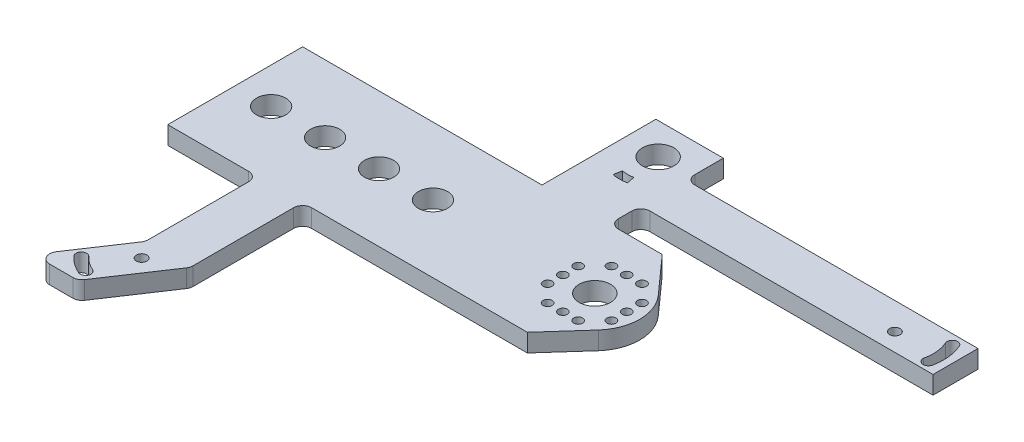
SolidWorks part; units mm, degrees
ref_plane "Front Plane" through (0, 0, 0) normal (0, 0, 1) x (1, 0, 0)
ref_plane "Top Plane" through (0, 0, 0) normal (0, 1, 0) x (1, 0, 0)
ref_plane "Right Plane" through (0, 0, 0) normal (1, 0, 0) x (0, 0, -1)
sketch "Sketch1" plane through (0, 0, 0) normal (0, 1, 0) x (1, 0, 0)
  circle A0 centre (0, 0) radius 10
  dimension "D1" = 20
extrude "Boss-Extrude1" add sketch "Sketch1" along normal blind 4
sketch "Sketch2" plane through (0, 0, 0) normal (0, 1, 0) x (1, 0, 0)
  line L0 (0, 0) -> (-40, 0) construction
  line L1 (-80, 15) -> (0, 15)
  line L2 (-80, 15) -> (-80, -15)
  line L3 (0, 15) -> (0, -15)
  line L4 (-80, -15) -> (0, -15)
  line L5 (0, 0) -> (-80, 0) construction
  line L6 (-40, 15) -> (-40, -15) construction
  line L7 (0, 15) -> (7.4536, 6.6667)
  line L8 (0, -15) -> (7.4536, -6.6667)
  line L9 (7.4536, 6.6667) -> (7.4536, -6.6667)
  circle A0 centre (0, 0) radius 10 construction
  dimension "D1" = 30
  dimension "D2" = 80
extrude "Boss-Extrude2" add sketch "Sketch2" along normal blind 4 contours L2 L4 L3 L1 | L9 L7 L3 L8
sketch "Sketch5" plane through (0, 0, 0) normal (0, 1, 0) x (1, 0, 0)
  line L0 (0, 0) -> (-19.25, 33.342) construction
  line L1 (-19.25, 33.342) -> (-19.25, 15) construction
  line L2 (-80, 15) -> (0, 15) construction
  line L3 (0, 0) -> (-80, 0) construction
  line L4 (-11.75, 40.342) -> (-26.75, 40.342)
  line L5 (-11.75, 40.342) -> (-11.75, 15)
  line L6 (-11.75, 15) -> (-26.75, 15)
  line L7 (-26.75, 40.342) -> (-26.75, 15)
  line L8 (-19.25, 15) -> (-19.25, 40.342) construction
  line L9 (-11.75, 27.671) -> (-26.75, 27.671) construction
  line L10 (-80, 15) -> (-80, -15) construction
  circle A0 centre (-19.25, 33.342) radius 11 construction
  circle A1 centre (0, 0) radius 27.5 construction
  circle A2 centre (-19.25, 33.342) radius 3.5
  point P5 (-19.25, 27.671)
  dimension "D2" = 22
  dimension "D3" = 55
  dimension "D7" = 7
  dimension "D1" = 38.5
  dimension "D4" = 15
  dimension "D5" = 7
  dimension "D6" = 60
extrude "Boss-Extrude3" add sketch "Sketch5" along normal blind 4
sketch "Sketch6" plane through (0, 4, 0) normal (0, 1, 0) x (1, 0, 0)
  line L0 (-19.25, 33.342) -> (-19.25, 25.012) construction
  line L1 (-20.6, 25.1221) -> (-20.3893, 26.4049) construction
  line L2 (-19.25, 25.012) -> (-19.25, 26.312) construction
  line L3 (-20.85, 24.9125) -> (-20.5143, 26.6809)
  line L4 (-19.25, 24.762) -> (-19.25, 26.562)
  circle A0 centre (-19.25, 33.342) radius 8.33 construction
  arc A1 (-19.25, 25.012) -> (-20.6, 25.1221) centre (-19.25, 33.342) cw construction
  arc A2 (-19.25, 26.312) -> (-20.3893, 26.4049) centre (-19.25, 33.342) cw construction
  arc A3 (-19.25, 24.762) -> (-20.85, 24.9125) centre (-19.25, 33.342) cw
  arc A4 (-19.25, 26.562) -> (-20.5143, 26.6809) centre (-19.25, 33.342) cw
  point P11 (0, 0)
  point P13 (0, 0)
  point P14 (0, 0)
  point P15 (-21.0225, 26.9125)
  dimension "D1" = 16.66
  dimension "D2" = 1.3
  dimension "D3" = 1.35
  dimension "D4" = 0.25
  dimension "D5" = 0.25
  dimension "D6" = 0.25
extrude "Cut-Extrude1" cut sketch "Sketch6" against normal through all contours L3 A4 L4 A3
ref_plane "Plane1" through (-19.25, 0, 0) normal (-1, 0, 0) x (0, 0, 1)
mirror "Mirror1" about plane through (-19.25, 0, 0) normal (-1, 0, 0) of "Cut-Extrude1"
sketch "Sketch7" plane through (0, 4, 0) normal (0, 1, 0) x (1, 0, 0)
  line L0 (-80, 0) -> (10, 0) construction
  line L1 (-80, 15) -> (-80, -15) construction
  arc A0 (7.4536, -6.6667) -> (7.4536, 6.6667) centre (0, 0) ccw construction
  circle A1 centre (-72, 0) radius 3.25
  dimension "D1" = 6.5
  dimension "D2" = 8
extrude "Cut-Extrude2" cut sketch "Sketch7" against normal through all
pattern_linear "LPattern1" count 4 spacing 12 along (1, 0, 0) of "Cut-Extrude2"
sketch "Sketch8" plane through (0, 0, 0) normal (0, 1, 0) x (1, 0, 0)
  line L0 (-26.75, 27) -> (20.75, 27) construction
  line L1 (-26.75, 40.342) -> (-26.75, 15) construction
  line L2 (-11.75, 15) -> (-11.75, 40.342) construction
  line L3 (53.25, 22) -> (-11.75, 22)
  line L4 (53.25, 22) -> (53.25, 32)
  line L5 (53.25, 32) -> (-11.75, 32)
  line L6 (-11.75, 22) -> (-11.75, 32)
  line L7 (20.75, 32) -> (20.75, 22) construction
  line L8 (53.25, 27) -> (-11.75, 27) construction
  line L9 (-80, 15) -> (-26.75, 15) construction
  dimension "D1" = 65
  dimension "D2" = 10
  dimension "D3" = 12
extrude "Boss-Extrude4" add sketch "Sketch8" along normal blind 4
sketch "Sketch9" plane through (0, 4, 0) normal (0, 1, 0) x (1, 0, 0)
  line L0 (53.25, 26) -> (40.75, 26) construction
  line L1 (53.25, 22) -> (53.25, 32) construction
  line L2 (-11.75, 22) -> (53.25, 22) construction
  line L3 (48.5662, 29.4302) -> (50.7181, 30.3746) construction
  line L4 (51.4453, 23.9728) -> (49.0547, 24.0272) construction
  circle A0 centre (40.75, 26) radius 1.175
  arc A1 (50.7181, 30.3746) -> (51.4453, 23.9728) centre (40.75, 26) cw
  arc A2 (48.5662, 29.4302) -> (49.0547, 24.0272) centre (40.75, 26) cw
  arc A3 (50.7181, 30.3746) -> (48.5662, 29.4302) centre (49.6422, 29.9024) ccw
  arc A4 (51.4453, 23.9728) -> (49.0547, 24.0272) centre (50.25, 24) cw
  dimension "D1" = 2.35
  dimension "D3" = 2.35
  dimension "D4" = 9.5
  dimension "D2" = 4
  dimension "D5" = 25
  dimension "D6" = 2
  dimension "D7" = 3
extrude "Cut-Extrude3" cut sketch "Sketch9" against normal blind 4
sketch "Sketch10" plane through (0, 0, 0) normal (0, 1, 0) x (1, 0, 0)
  line L0 (-55, -15) -> (-55, -27.5) construction
  line L1 (-80, -15) -> (0, -15) construction
  line L2 (-80, 15) -> (-80, -15) construction
  line L3 (-60, -40) -> (-50, -40)
  line L4 (-60, -40) -> (-60, -15)
  line L5 (-60, -15) -> (-50, -15)
  line L6 (-50, -40) -> (-50, -15)
  line L7 (-55, -15) -> (-55, -40) construction
  line L8 (-60, -27.5) -> (-50, -27.5) construction
  line L9 (-50, -40) -> (-60, -55)
  line L10 (-60, -55) -> (-60, -40)
  line L11 (-60, -40) -> (-70, -55)
  line L12 (-70, -55) -> (-60, -55)
  dimension "D1" = 25
  dimension "D2" = 10
  dimension "D3" = 25
  dimension "D4" = 15
extrude "Boss-Extrude5" add sketch "Sketch10" along normal blind 4 contours L10 L9 L3 | L3 L6 L5 L4 | L11 L12 L10
sketch "Sketch11" plane through (0, 4, 0) normal (0, 1, 0) x (1, 0, 0)
  line L0 (-60, -47.7889) -> (-50, -32.7889) construction
  line L1 (-60, -40) -> (-60, -15) construction
  line L2 (-50, -40) -> (-50, -15) construction
  line L3 (-50, -40) -> (-60, -55) construction
  line L4 (-61.3636, -53.4398) -> (-60.4494, -51.2749) construction
  line L5 (-65.1307, -50.7635) -> (-63.3872, -49.1877) construction
  line L7 (-50, -40) -> (-60, -55) construction
  circle A0 centre (-57.2111, -43.6056) radius 1.175
  arc A1 (-61.3636, -53.4398) -> (-65.1307, -50.7635) centre (-57.2111, -43.6056) cw
  arc A2 (-60.4494, -51.2749) -> (-63.3872, -49.1877) centre (-57.2111, -43.6056) cw
  arc A3 (-65.1307, -50.7635) -> (-63.3872, -49.1877) centre (-64.2589, -49.9756) cw
  arc A4 (-60.4494, -51.2749) -> (-61.3636, -53.4398) centre (-60.9065, -52.3573) cw
  dimension "D1" = 2.35
  dimension "D3" = 1.175
  dimension "D7" = 13
  dimension "D2" = 4
  dimension "D4" = 9.5
  dimension "D5" = 25
  dimension "D6" = 2
extrude "Cut-Extrude4" cut sketch "Sketch11" against normal blind 4
sketch "Sketch12" plane through (0, 4, 0) normal (0, 1, 0) x (1, 0, 0)
  line L0 (0, 0) -> (10, 0) construction
  line L1 (7.1, 3.4) -> (7.1, -3.4) construction
  circle A0 centre (0, 0) radius 10 construction
  arc A1 (7.4536, -6.6667) -> (7.4536, 6.6667) centre (0, 0) ccw construction
  circle A2 centre (7.1, 3.4) radius 1
  circle A3 centre (7.1, -3.4) radius 1
  circle A4 centre (7.1, 0) radius 1
  point P11 (7.1, 0)
  dimension "D1" = 2
  dimension "D2" = 6.8
  dimension "D3" = 7.1
extrude "Cut-Extrude5" cut sketch "Sketch12" against normal through all
pattern_circular "CirPattern1" count 4 over 360 about axis through (0, 0, 0) along (0, 1, 0) of "Cut-Extrude5"
sketch "Sketch13" plane through (0, 4, 0) normal (0, 1, 0) x (1, 0, 0)
  circle A0 centre (0, 0) radius 3.5
  dimension "D1" = 7
extrude "Cut-Extrude6" cut sketch "Sketch13" against normal through all
fillet "Fillet1" radius 2 9 edges at (-60, 2, 55) (-50, 2, 40) (-60, 2, 40) (-60, 2, 15) (-50, 2, 15) (-11.75, 2, -32) (-11.75, 2, -15) (-11.75, 2, -22) (-70, 2, 55)
